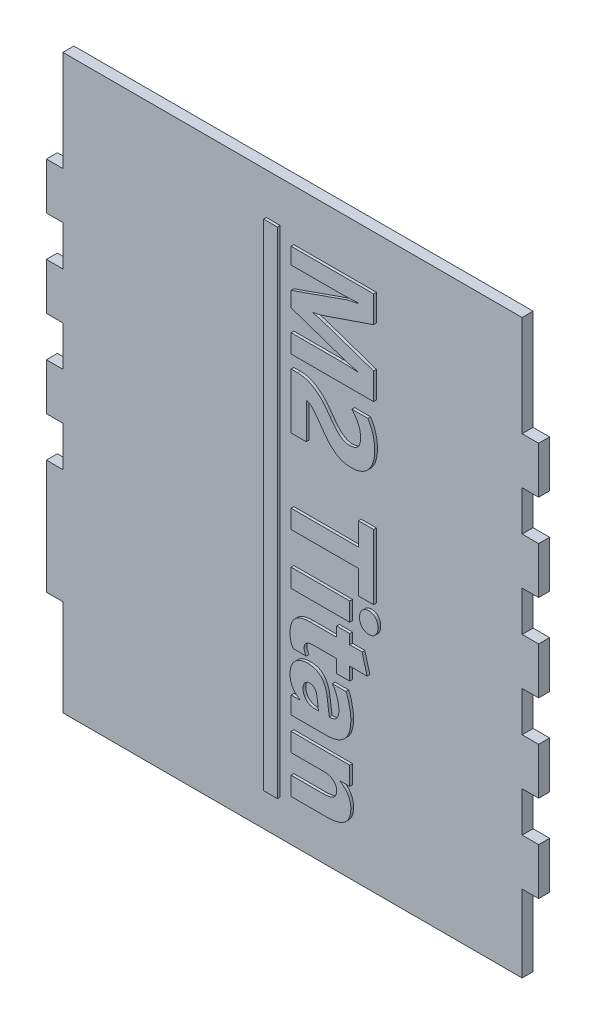
SolidWorks part; units mm, degrees
ref_plane "Front Plane" through (0, 0, 0) normal (0, 0, 1) x (1, 0, 0)
ref_plane "Top Plane" through (0, 0, 0) normal (0, 1, 0) x (1, 0, 0)
ref_plane "Right Plane" through (0, 0, 0) normal (1, 0, 0) x (0, 0, -1)
sketch "Sketch1" plane through (0, 0, 0) normal (0, 0, 1) x (1, 0, 0)
  line L1 (0, 0) -> (113.665, 0)
  line L2 (0, 0) -> (0, 132.08)
  line L3 (0, 132.08) -> (113.665, 132.08)
  line L4 (113.665, 0) -> (113.665, 132.08)
  dimension "D1" = 132.08
  dimension "D2" = 113.665
extrude "Boss-Extrude1" add sketch "Sketch1" along normal blind 2.54
sketch "Sketch2" plane through (0, 0, 2.54) normal (0, 0, 1) x (1, 0, 0)
  line L0 (0, 132.08) -> (113.665, 132.08) construction
  line L1 (0, 132.08) -> (0, 0) construction
  line L2 (0, 0) -> (113.665, 0) construction
  line L3 (0, 0) -> (113.665, 0) construction
  line L4 (113.665, 0) -> (113.665, 132.08) construction
  line L5 (0, 132.08) -> (0, 0) construction
  line L6 (113.665, 132.08) -> (0, 132.08) construction
  line L7 (0, 0) -> (3.81, 0)
  line L8 (0, 0) -> (0, 22.225)
  line L9 (0, 132.08) -> (3.81, 132.08)
  line L10 (0, 132.08) -> (0, 108.839)
  line L11 (0, 108.839) -> (3.81, 108.839)
  line L12 (3.81, 132.08) -> (3.81, 108.839)
  line L13 (0, 98.044) -> (3.81, 98.044)
  line L14 (0, 98.044) -> (0, 88.773)
  line L15 (0, 88.773) -> (3.81, 88.773)
  line L16 (3.81, 98.044) -> (3.81, 88.773)
  line L17 (0, 77.978) -> (3.81, 77.978)
  line L18 (0, 77.978) -> (0, 68.707)
  line L19 (0, 68.707) -> (3.81, 68.707)
  line L20 (3.81, 77.978) -> (3.81, 68.707)
  line L21 (0, 57.912) -> (3.81, 57.912)
  line L22 (0, 57.912) -> (0, 48.641)
  line L23 (0, 48.641) -> (3.81, 48.641)
  line L24 (3.81, 57.912) -> (3.81, 48.641)
  line L25 (109.855, 132.7665) -> (109.855, -10.5896) construction
  line L26 (113.665, 132.08) -> (109.855, 132.08)
  line L27 (113.665, 132.08) -> (113.665, 108.839)
  line L28 (113.665, 108.839) -> (109.855, 108.839)
  line L29 (109.855, 132.08) -> (109.855, 108.839)
  line L30 (113.665, 98.044) -> (109.855, 98.044)
  line L31 (113.665, 98.044) -> (113.665, 88.773)
  line L32 (113.665, 88.773) -> (109.855, 88.773)
  line L33 (109.855, 98.044) -> (109.855, 88.773)
  line L34 (113.665, 77.978) -> (109.855, 77.978)
  line L35 (113.665, 77.978) -> (113.665, 68.707)
  line L36 (113.665, 68.707) -> (109.855, 68.707)
  line L37 (109.855, 77.978) -> (109.855, 68.707)
  line L38 (113.665, 57.912) -> (109.855, 57.912)
  line L39 (113.665, 57.912) -> (113.665, 48.641)
  line L40 (113.665, 48.641) -> (109.855, 48.641)
  line L41 (109.855, 57.912) -> (109.855, 48.641)
  line L42 (113.665, 37.846) -> (109.855, 37.846)
  line L43 (113.665, 37.846) -> (113.665, 28.575)
  line L44 (113.665, 28.575) -> (109.855, 28.575)
  line L45 (109.855, 37.846) -> (109.855, 28.575)
  line L46 (113.665, 17.78) -> (109.855, 17.78)
  line L47 (113.665, 17.78) -> (113.665, 0)
  line L48 (113.665, 0) -> (109.855, 0)
  line L49 (109.855, 17.78) -> (109.855, 0)
  line L50 (0, 22.225) -> (3.81, 22.225)
  line L51 (3.81, 0) -> (3.81, 22.225)
  dimension "D1" = 113.665
  dimension "D2" = 22.225
  dimension "D4" = 23.241
  dimension "D5" = 9.271
  dimension "D6" = 3.81
  dimension "D8" = 3.81
  dimension "D9" = 23.241
  dimension "D10" = 10.795
  dimension "D11" = 10.795
  dimension "D12" = 10.795
  dimension "D13" = 10.795
  dimension "D14" = 10.795
  dimension "D15" = 10.795
  dimension "D16" = 10.795
  dimension "D17" = 10.795
extrude "Cut-Extrude1" cut sketch "Sketch2" against normal blind 3.81
sketch "Sketch5" plane through (0, 0, 2.54) normal (0, 0, 1) x (1, 0, 0)
  line L0 (57.15, 122.555) -> (57.15, 7.4832) construction
  line L1 (0, 132.08) -> (0, 0) construction
  line L2 (109.855, 132.08) -> (3.81, 132.08) construction
  line L4 (53.975, 122.555) -> (50.8, 122.555)
  line L5 (53.975, 122.555) -> (53.975, 8.255)
  line L6 (53.975, 8.255) -> (50.8, 8.255)
  line L7 (50.8, 122.555) -> (50.8, 8.255)
  text T0 "M2 Titan" font "Gadugi" height 19.05
  dimension "D1" = 57.15
  dimension "D2" = 9.525
  dimension "D3" = 114.3
  dimension "D4" = 3.175
  dimension "D5" = 9.525
  dimension "D6" = 50.8
extrude "Boss-Extrude2" add sketch "Sketch5" along normal blind 0.635
